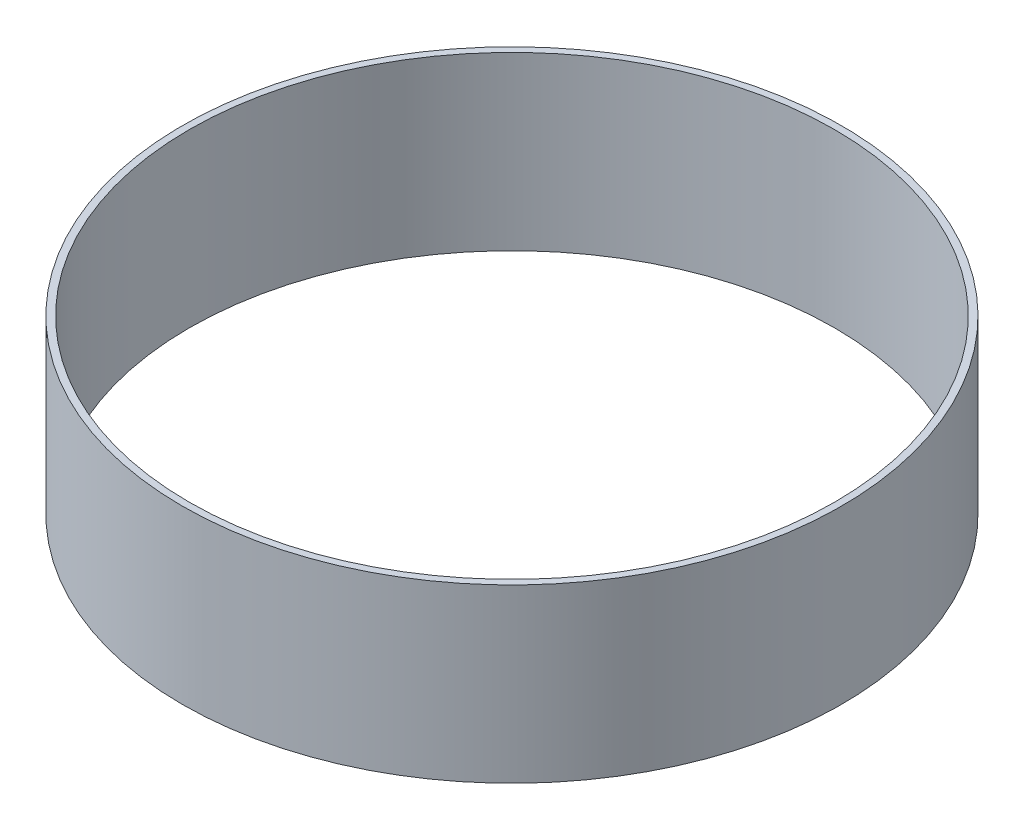
SolidWorks part; units mm, degrees
ref_plane "Front Plane" through (0, 0, 0) normal (0, 0, 1) x (1, 0, 0)
ref_plane "Top Plane" through (0, 0, 0) normal (0, 1, 0) x (1, 0, 0)
ref_plane "Right Plane" through (0, 0, 0) normal (1, 0, 0) x (0, 0, -1)
sketch "Sketch1" plane through (0, 0, 0) normal (0, 1, 0) x (1, 0, 0)
  circle A0 centre (0, 0) radius 95.4405
  circle A1 centre (0, 0) radius 97.4725
  dimension "D1" = 190.881
  dimension "D2" = 194.945
extrude "Boss-Extrude1" add sketch "Sketch1" along normal blind 50.8
